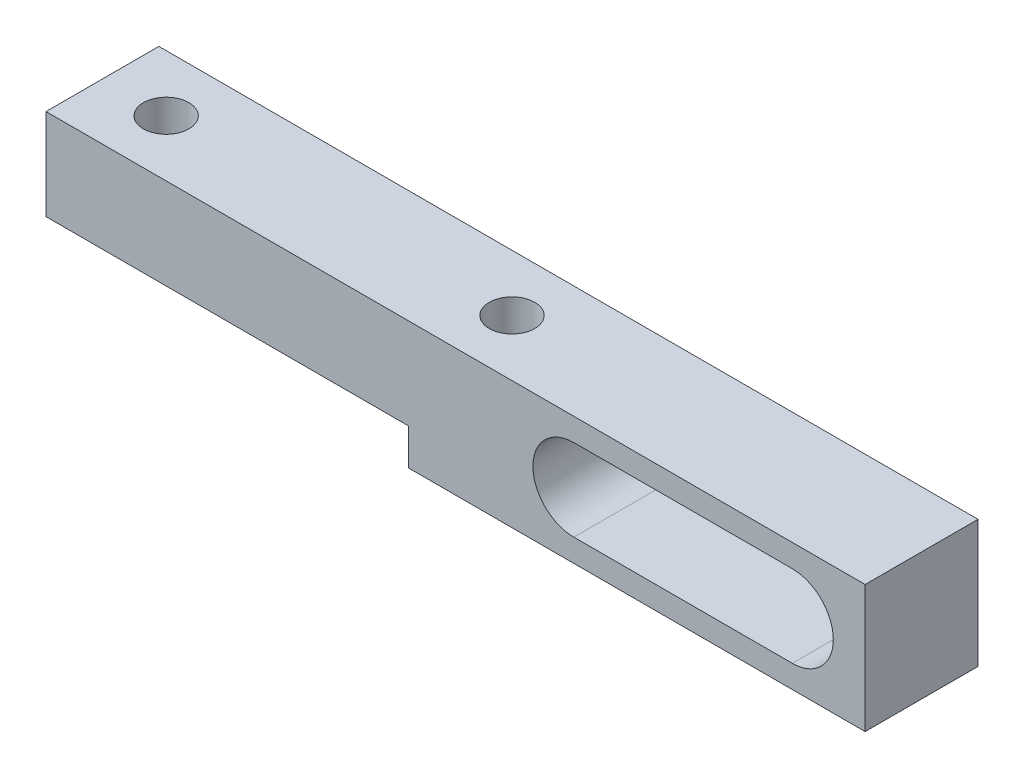
SolidWorks part; units mm, degrees
ref_plane "前视基准面" through (0, 0, 0) normal (0, 0, 1) x (1, 0, 0)
ref_plane "上视基准面" through (0, 0, 0) normal (0, 1, 0) x (1, 0, 0)
ref_plane "右视基准面" through (0, 0, 0) normal (1, 0, 0) x (0, 0, -1)
sketch "草图1" plane through (0, 0, 0) normal (0, 0, 1) x (1, 0, 0)
  line L0 (45, 5) -> (0, 5)
  line L1 (19.9248, -2) -> (45, -2)
  line L2 (19.9248, 0) -> (19.9248, -2)
  line L3 (19.9248, 0) -> (0, 0)
  line L4 (29, -0.75) -> (41, -0.75)
  line L5 (41, 3.75) -> (29, 3.75)
  line L6 (45, -2) -> (45, 5)
  line L7 (0, 0) -> (0, 5)
  line L9 (4.75, 0) -> (4.75, 5) construction
  line L11 (23.75, -2) -> (23.75, 5) construction
  line L16 (26.525, 1.5) -> (31.475, 1.5) construction
  line L17 (29, -0.975) -> (29, 3.975) construction
  line L18 (38.525, 1.5) -> (43.475, 1.5) construction
  arc A0 (41, -0.75) -> (41, 3.75) centre (41, 1.5) ccw
  arc A1 (29, 3.75) -> (29, -0.75) centre (29, 1.5) ccw
extrude "凸台-拉伸2" add sketch "草图1" along normal blind 6.2
hole_wizard "M3 螺纹孔1" positions "草图2" profile "草图4" tap size "M3" standard "ISO" end condition through all
sketch "草图2" plane through (0, -2, 0) normal (0, -1, 0) x (-1, 0, 0)
  line L0 (-19.9248, -6.2) -> (-45, -6.2) construction
  line L1 (-45, -6.2) -> (-45, 0) construction
  point P0 (-22.5, -3.1)
  point P2 (-3.5, -3.1)
  dimension "D1" = 3.1
  dimension "D2" = 22.5
  dimension "D3" = 41.5
sketch "草图4" plane through (22.5, -2, 3.1) normal (1, 0, 0) x (0, 0, -1)
  line L0 (0, 0) -> (0, 7)
  line L1 (0, 7) -> (1.25, 7)
  line L2 (1.25, 7) -> (1.25, 0)
  line L5 (1.25, 0) -> (0, 0)
  line L11 (0, -6.35) -> (0, 107.95) construction
  dimension "通孔螺纹孔钻头直径" = 2.5
  dimension "通孔螺纹孔钻头深度" = 7
cosmetic thread "孔螺蚊线1" parameters "D2"=3
cosmetic thread "孔螺蚊线2" parameters "D2"=3
